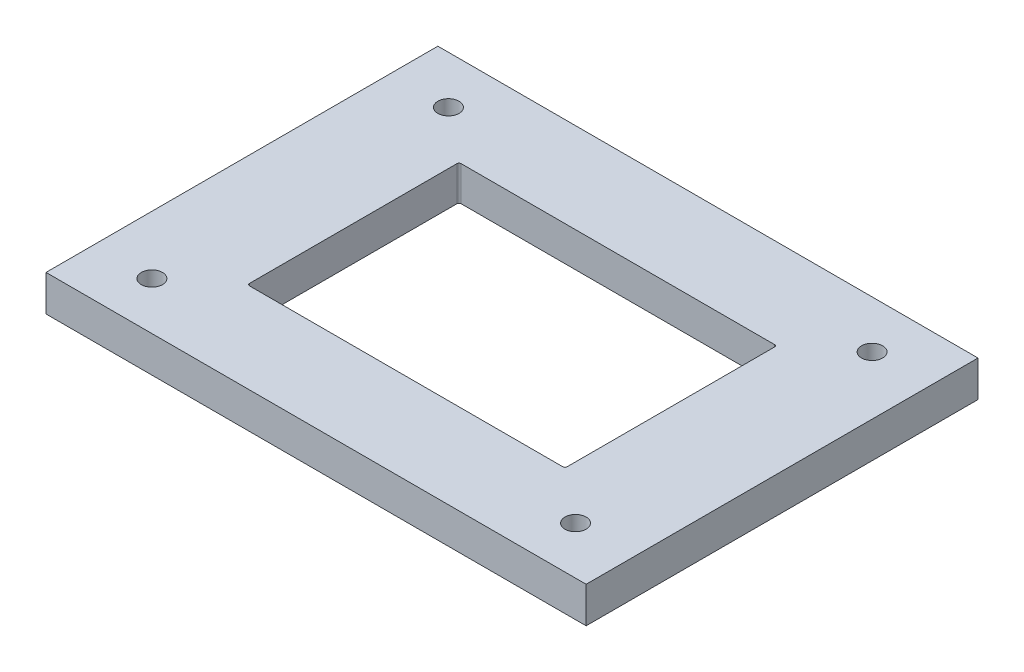
SolidWorks part; units mm, degrees
ref_plane "Front Plane" through (0, 0, 0) normal (0, 0, 1) x (1, 0, 0)
ref_plane "Top Plane" through (0, 0, 0) normal (0, 1, 0) x (1, 0, 0)
ref_plane "Right Plane" through (0, 0, 0) normal (1, 0, 0) x (0, 0, -1)
sketch "Sketch1" plane through (0, 0, 0) normal (0, 1, 0) x (1, 0, 0)
  line L1 (127.5, -92.5) -> (-127.5, -92.5)
  line L2 (127.5, -92.5) -> (127.5, 92.5)
  line L3 (127.5, 92.5) -> (-127.5, 92.5)
  line L4 (-127.5, -92.5) -> (-127.5, 92.5)
  line L5 (127.5, -92.5) -> (-127.5, 92.5) construction
  line L6 (127.5, 92.5) -> (-127.5, -92.5) construction
  point P0 (0, 0)
  dimension "D1" = 255
  dimension "D2" = 185
extrude "Boss-Extrude1" add sketch "Sketch1" against normal blind 17
sketch "Sketch2" plane through (0, 0, 0) normal (0, 1, 0) x (1, 0, 0)
  line L1 (74.97, -49.97) -> (-74.97, -49.97)
  line L2 (74.97, -49.97) -> (74.97, 49.97)
  line L3 (74.97, 49.97) -> (-74.97, 49.97)
  line L4 (-74.97, -49.97) -> (-74.97, 49.97)
  line L5 (74.97, -49.97) -> (-74.97, 49.97) construction
  line L6 (74.97, 49.97) -> (-74.97, -49.97) construction
  point P0 (0, 0)
  dimension "D1" = 149.94
  dimension "D2" = 99.94
extrude "Cut-Extrude1" cut sketch "Sketch2" against normal blind 19.5 draft 2 draft outward yes
fillet "Fillet1" radius 1 4 edges at (75.2668, -8.5, 50.2668) (-75.2668, -8.5, 50.2668) (75.2668, -8.5, -50.2668) (-75.2668, -8.5, -50.2668)
sketch "Sketch3" plane through (0, 0, 0) normal (0, 1, 0) x (1, 0, 0)
  line L0 (0, 0) -> (0, 50000) construction
  line L1 (0, 0) -> (-50000, 0) construction
  circle A0 centre (-100, 70) radius 5
  circle A1 centre (100, 70) radius 5
  circle A2 centre (100, -70) radius 5
  circle A3 centre (-100, -70) radius 5
  dimension "D3" = 10
  dimension "D1" = 100
  dimension "D2" = 70
extrude "Cut-Extrude2" cut sketch "Sketch3" against normal blind 19.5
